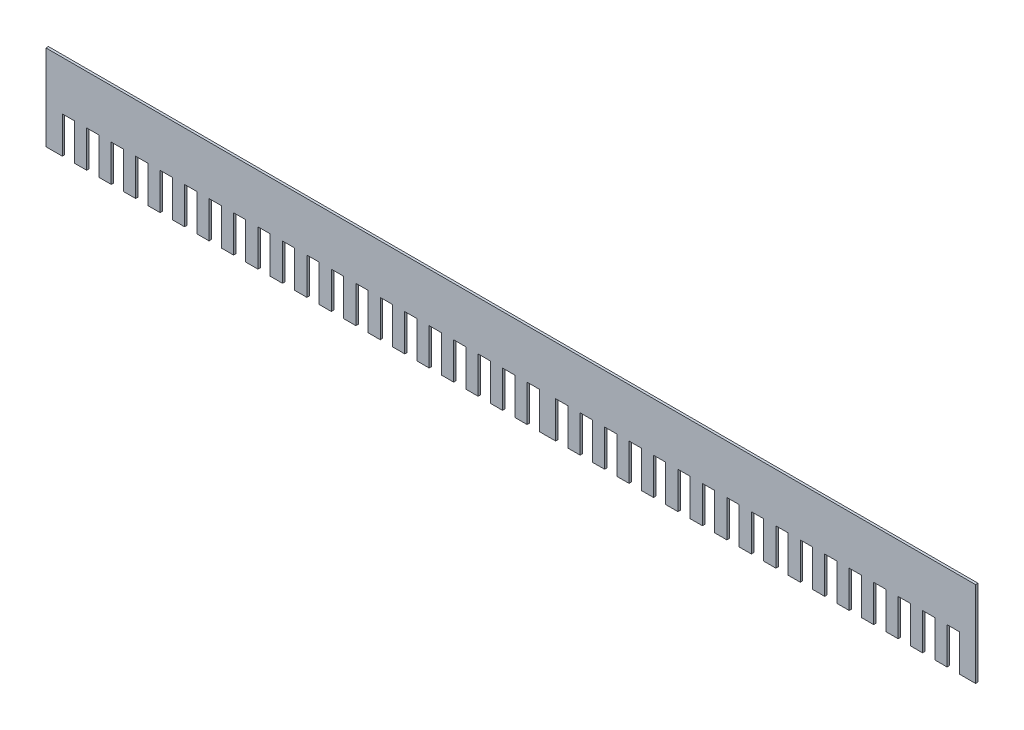
SolidWorks part; units mm, degrees
ref_plane "Front Plane" through (0, 0, 0) normal (0, 0, 1) x (1, 0, 0)
ref_plane "Top Plane" through (0, 0, 0) normal (0, 1, 0) x (1, 0, 0)
ref_plane "Right Plane" through (0, 0, 0) normal (1, 0, 0) x (0, 0, -1)
sketch "Sketch1" plane through (0, 0, 0) normal (0, 0, 1) x (1, 0, 0)
  line L0 (-180.8196, -15.4651) -> (-180.8196, -0.4651)
  line L1 (-202.4725, 19.5349) -> (177.5275, 19.5349)
  line L2 (-202.4725, 19.5349) -> (-202.4725, -15.4651)
  line L3 (-202.4725, -15.4651) -> (177.5275, -15.4651)
  line L5 (-195.8196, -15.4651) -> (-190.8196, -15.4651)
  line L6 (-195.8196, -15.4651) -> (-195.8196, -0.4651)
  line L7 (-195.8196, -0.4651) -> (-190.8196, -0.4651)
  line L8 (-190.8196, -15.4651) -> (-190.8196, -0.4651)
  line L9 (-185.8196, -15.4651) -> (-185.8196, -0.4651)
  line L10 (-185.8196, -0.4651) -> (-180.8196, -0.4651)
  line L11 (-180.8196, -15.4651) -> (-180.8196, -0.4651)
  line L12 (-185.8196, -15.4651) -> (-185.8196, -0.4651)
  line L13 (-185.8196, -0.4651) -> (-180.8196, -0.4651)
  line L14 (-175.8196, -15.4651) -> (-175.8196, -0.4651)
  line L15 (-175.8196, -0.4651) -> (-170.8196, -0.4651)
  line L16 (-170.8196, -15.4651) -> (-170.8196, -0.4651)
  line L17 (-180.8196, -15.4651) -> (-180.8196, -0.4651)
  line L18 (-185.8196, -15.4651) -> (-185.8196, -0.4651)
  line L19 (-185.8196, -0.4651) -> (-180.8196, -0.4651)
  line L20 (-175.8196, -15.4651) -> (-175.8196, -0.4651)
  line L21 (-175.8196, -0.4651) -> (-170.8196, -0.4651)
  line L22 (-170.8196, -15.4651) -> (-170.8196, -0.4651)
  line L23 (-165.8196, -15.4651) -> (-165.8196, -0.4651)
  line L24 (-165.8196, -0.4651) -> (-160.8196, -0.4651)
  line L25 (-160.8196, -15.4651) -> (-160.8196, -0.4651)
  line L26 (-180.8196, -15.4651) -> (-180.8196, -0.4651)
  line L27 (-185.8196, -15.4651) -> (-185.8196, -0.4651)
  line L28 (-185.8196, -0.4651) -> (-180.8196, -0.4651)
  line L29 (-175.8196, -15.4651) -> (-175.8196, -0.4651)
  line L30 (-175.8196, -0.4651) -> (-170.8196, -0.4651)
  line L31 (-170.8196, -15.4651) -> (-170.8196, -0.4651)
  line L32 (-165.8196, -15.4651) -> (-165.8196, -0.4651)
  line L33 (-165.8196, -0.4651) -> (-160.8196, -0.4651)
  line L34 (-160.8196, -15.4651) -> (-160.8196, -0.4651)
  line L35 (-155.8196, -15.4651) -> (-155.8196, -0.4651)
  line L36 (-155.8196, -0.4651) -> (-150.8196, -0.4651)
  line L37 (-150.8196, -15.4651) -> (-150.8196, -0.4651)
  line L38 (-145.8196, -15.4651) -> (-145.8196, -0.4651)
  line L39 (-145.8196, -0.4651) -> (-140.8196, -0.4651)
  line L40 (-140.8196, -15.4651) -> (-140.8196, -0.4651)
  line L41 (-135.8196, -15.4651) -> (-135.8196, -0.4651)
  line L42 (-135.8196, -0.4651) -> (-130.8196, -0.4651)
  line L43 (-130.8196, -15.4651) -> (-130.8196, -0.4651)
  line L44 (-135.8196, -15.4651) -> (-135.8196, -0.4651)
  line L45 (-135.8196, -0.4651) -> (-130.8196, -0.4651)
  line L46 (-130.8196, -15.4651) -> (-130.8196, -0.4651)
  line L47 (-125.8196, -15.4651) -> (-125.8196, -0.4651)
  line L48 (-125.8196, -0.4651) -> (-120.8196, -0.4651)
  line L49 (-120.8196, -15.4651) -> (-120.8196, -0.4651)
  line L50 (-135.8196, -15.4651) -> (-135.8196, -0.4651)
  line L51 (-135.8196, -0.4651) -> (-130.8196, -0.4651)
  line L52 (-130.8196, -15.4651) -> (-130.8196, -0.4651)
  line L53 (-125.8196, -15.4651) -> (-125.8196, -0.4651)
  line L54 (-125.8196, -0.4651) -> (-120.8196, -0.4651)
  line L55 (-120.8196, -15.4651) -> (-120.8196, -0.4651)
  line L56 (-115.8196, -15.4651) -> (-115.8196, -0.4651)
  line L57 (-115.8196, -0.4651) -> (-110.8196, -0.4651)
  line L58 (-110.8196, -15.4651) -> (-110.8196, -0.4651)
  line L59 (-105.8196, -15.4651) -> (-105.8196, -0.4651)
  line L60 (-105.8196, -0.4651) -> (-100.8196, -0.4651)
  line L61 (-100.8196, -15.4651) -> (-100.8196, -0.4651)
  line L62 (-95.8196, -15.4651) -> (-95.8196, -0.4651)
  line L63 (-95.8196, -0.4651) -> (-90.8196, -0.4651)
  line L64 (-90.8196, -15.4651) -> (-90.8196, -0.4651)
  line L65 (-105.8196, -15.4651) -> (-105.8196, -0.4651)
  line L66 (-100.8196, -15.4651) -> (-100.8196, -0.4651)
  line L67 (-85.8196, -15.4651) -> (-85.8196, -0.4651)
  line L68 (-85.8196, -0.4651) -> (-80.8196, -0.4651)
  line L69 (-80.8196, -15.4651) -> (-80.8196, -0.4651)
  line L70 (-85.8196, -15.4651) -> (-85.8196, -0.4651)
  line L71 (-85.8196, -0.4651) -> (-80.8196, -0.4651)
  line L72 (-80.8196, -15.4651) -> (-80.8196, -0.4651)
  line L73 (-75.8196, -15.4651) -> (-75.8196, -0.4651)
  line L74 (-75.8196, -0.4651) -> (-70.8196, -0.4651)
  line L75 (-70.8196, -15.4651) -> (-70.8196, -0.4651)
  line L76 (-85.8196, -15.4651) -> (-85.8196, -0.4651)
  line L77 (-85.8196, -0.4651) -> (-80.8196, -0.4651)
  line L78 (-80.8196, -15.4651) -> (-80.8196, -0.4651)
  line L79 (-75.8196, -15.4651) -> (-75.8196, -0.4651)
  line L80 (-75.8196, -0.4651) -> (-70.8196, -0.4651)
  line L81 (-70.8196, -15.4651) -> (-70.8196, -0.4651)
  line L82 (-65.8196, -15.4651) -> (-65.8196, -0.4651)
  line L83 (-65.8196, -0.4651) -> (-60.8196, -0.4651)
  line L84 (-60.8196, -15.4651) -> (-60.8196, -0.4651)
  line L85 (-85.8196, -15.4651) -> (-85.8196, -0.4651)
  line L86 (-85.8196, -0.4651) -> (-80.8196, -0.4651)
  line L87 (-80.8196, -15.4651) -> (-80.8196, -0.4651)
  line L88 (-75.8196, -15.4651) -> (-75.8196, -0.4651)
  line L89 (-75.8196, -0.4651) -> (-70.8196, -0.4651)
  line L90 (-70.8196, -15.4651) -> (-70.8196, -0.4651)
  line L91 (-65.8196, -15.4651) -> (-65.8196, -0.4651)
  line L92 (-65.8196, -0.4651) -> (-60.8196, -0.4651)
  line L93 (-60.8196, -15.4651) -> (-60.8196, -0.4651)
  line L94 (-55.8196, -15.4651) -> (-55.8196, -0.4651)
  line L95 (-55.8196, -0.4651) -> (-50.8196, -0.4651)
  line L96 (-50.8196, -15.4651) -> (-50.8196, -0.4651)
  line L97 (-85.8196, -15.4651) -> (-85.8196, -0.4651)
  line L98 (-85.8196, -0.4651) -> (-80.8196, -0.4651)
  line L99 (-80.8196, -15.4651) -> (-80.8196, -0.4651)
  line L100 (-75.8196, -15.4651) -> (-75.8196, -0.4651)
  line L101 (-75.8196, -0.4651) -> (-70.8196, -0.4651)
  line L102 (-70.8196, -15.4651) -> (-70.8196, -0.4651)
  line L103 (-65.8196, -15.4651) -> (-65.8196, -0.4651)
  line L104 (-65.8196, -0.4651) -> (-60.8196, -0.4651)
  line L105 (-60.8196, -15.4651) -> (-60.8196, -0.4651)
  line L106 (-55.8196, -15.4651) -> (-55.8196, -0.4651)
  line L107 (-55.8196, -0.4651) -> (-50.8196, -0.4651)
  line L108 (-50.8196, -15.4651) -> (-50.8196, -0.4651)
  line L109 (-45.8196, -15.4651) -> (-45.8196, -0.4651)
  line L110 (-45.8196, -0.4651) -> (-40.8196, -0.4651)
  line L111 (-40.8196, -15.4651) -> (-40.8196, -0.4651)
  line L112 (-85.8196, -15.4651) -> (-85.8196, -0.4651)
  line L113 (-85.8196, -0.4651) -> (-80.8196, -0.4651)
  line L114 (-80.8196, -15.4651) -> (-80.8196, -0.4651)
  line L115 (-75.8196, -15.4651) -> (-75.8196, -0.4651)
  line L116 (-75.8196, -0.4651) -> (-70.8196, -0.4651)
  line L117 (-70.8196, -15.4651) -> (-70.8196, -0.4651)
  line L118 (-65.8196, -15.4651) -> (-65.8196, -0.4651)
  line L119 (-65.8196, -0.4651) -> (-60.8196, -0.4651)
  line L120 (-60.8196, -15.4651) -> (-60.8196, -0.4651)
  line L121 (-55.8196, -15.4651) -> (-55.8196, -0.4651)
  line L122 (-55.8196, -0.4651) -> (-50.8196, -0.4651)
  line L123 (-50.8196, -15.4651) -> (-50.8196, -0.4651)
  line L124 (-45.8196, -15.4651) -> (-45.8196, -0.4651)
  line L125 (-45.8196, -0.4651) -> (-40.8196, -0.4651)
  line L126 (-40.8196, -15.4651) -> (-40.8196, -0.4651)
  line L127 (-35.8196, -15.4651) -> (-35.8196, -0.4651)
  line L128 (-35.8196, -0.4651) -> (-30.8196, -0.4651)
  line L129 (-30.8196, -15.4651) -> (-30.8196, -0.4651)
  line L130 (-12.4725, 19.5349) -> (-12.4725, -15.4651) construction
  line L131 (5.8747, -15.4651) -> (5.8747, -0.4651)
  line L132 (10.8747, -0.4651) -> (5.8747, -0.4651)
  line L133 (10.8747, -15.4651) -> (10.8747, -0.4651)
  line L134 (15.8747, -15.4651) -> (15.8747, -0.4651)
  line L135 (20.8747, -0.4651) -> (15.8747, -0.4651)
  line L136 (20.8747, -15.4651) -> (20.8747, -0.4651)
  line L137 (25.8747, -15.4651) -> (25.8747, -0.4651)
  line L138 (30.8747, -0.4651) -> (25.8747, -0.4651)
  line L139 (30.8747, -15.4651) -> (30.8747, -0.4651)
  line L140 (35.8747, -15.4651) -> (35.8747, -0.4651)
  line L141 (40.8747, -0.4651) -> (35.8747, -0.4651)
  line L142 (40.8747, -15.4651) -> (40.8747, -0.4651)
  line L143 (45.8747, -15.4651) -> (45.8747, -0.4651)
  line L144 (50.8747, -0.4651) -> (45.8747, -0.4651)
  line L145 (50.8747, -15.4651) -> (50.8747, -0.4651)
  line L146 (55.8747, -15.4651) -> (55.8747, -0.4651)
  line L147 (60.8747, -0.4651) -> (55.8747, -0.4651)
  line L148 (60.8747, -15.4651) -> (60.8747, -0.4651)
  line L149 (15.8747, -15.4651) -> (15.8747, -0.4651)
  line L150 (20.8747, -0.4651) -> (15.8747, -0.4651)
  line L151 (20.8747, -15.4651) -> (20.8747, -0.4651)
  line L152 (25.8747, -15.4651) -> (25.8747, -0.4651)
  line L153 (30.8747, -0.4651) -> (25.8747, -0.4651)
  line L154 (30.8747, -15.4651) -> (30.8747, -0.4651)
  line L155 (35.8747, -15.4651) -> (35.8747, -0.4651)
  line L156 (40.8747, -0.4651) -> (35.8747, -0.4651)
  line L157 (40.8747, -15.4651) -> (40.8747, -0.4651)
  line L158 (45.8747, -15.4651) -> (45.8747, -0.4651)
  line L159 (50.8747, -0.4651) -> (45.8747, -0.4651)
  line L160 (50.8747, -15.4651) -> (50.8747, -0.4651)
  line L161 (55.8747, -15.4651) -> (55.8747, -0.4651)
  line L162 (60.8747, -0.4651) -> (55.8747, -0.4651)
  line L163 (60.8747, -15.4651) -> (60.8747, -0.4651)
  line L164 (25.8747, -15.4651) -> (25.8747, -0.4651)
  line L165 (30.8747, -0.4651) -> (25.8747, -0.4651)
  line L166 (30.8747, -15.4651) -> (30.8747, -0.4651)
  line L167 (35.8747, -15.4651) -> (35.8747, -0.4651)
  line L168 (40.8747, -0.4651) -> (35.8747, -0.4651)
  line L169 (40.8747, -15.4651) -> (40.8747, -0.4651)
  line L170 (45.8747, -15.4651) -> (45.8747, -0.4651)
  line L171 (50.8747, -0.4651) -> (45.8747, -0.4651)
  line L172 (50.8747, -15.4651) -> (50.8747, -0.4651)
  line L173 (55.8747, -15.4651) -> (55.8747, -0.4651)
  line L174 (60.8747, -0.4651) -> (55.8747, -0.4651)
  line L175 (60.8747, -15.4651) -> (60.8747, -0.4651)
  line L176 (35.8747, -15.4651) -> (35.8747, -0.4651)
  line L177 (40.8747, -0.4651) -> (35.8747, -0.4651)
  line L178 (40.8747, -15.4651) -> (40.8747, -0.4651)
  line L179 (45.8747, -15.4651) -> (45.8747, -0.4651)
  line L180 (50.8747, -0.4651) -> (45.8747, -0.4651)
  line L181 (50.8747, -15.4651) -> (50.8747, -0.4651)
  line L182 (55.8747, -15.4651) -> (55.8747, -0.4651)
  line L183 (60.8747, -0.4651) -> (55.8747, -0.4651)
  line L184 (60.8747, -15.4651) -> (60.8747, -0.4651)
  line L185 (45.8747, -15.4651) -> (45.8747, -0.4651)
  line L186 (50.8747, -0.4651) -> (45.8747, -0.4651)
  line L187 (50.8747, -15.4651) -> (50.8747, -0.4651)
  line L188 (55.8747, -15.4651) -> (55.8747, -0.4651)
  line L189 (60.8747, -0.4651) -> (55.8747, -0.4651)
  line L190 (60.8747, -15.4651) -> (60.8747, -0.4651)
  line L191 (55.8747, -15.4651) -> (55.8747, -0.4651)
  line L192 (60.8747, -0.4651) -> (55.8747, -0.4651)
  line L193 (60.8747, -15.4651) -> (60.8747, -0.4651)
  line L194 (75.8747, -15.4651) -> (75.8747, -0.4651)
  line L195 (80.8747, -15.4651) -> (80.8747, -0.4651)
  line L196 (65.8747, -15.4651) -> (65.8747, -0.4651)
  line L197 (70.8747, -0.4651) -> (65.8747, -0.4651)
  line L198 (70.8747, -15.4651) -> (70.8747, -0.4651)
  line L199 (75.8747, -15.4651) -> (75.8747, -0.4651)
  line L200 (80.8747, -0.4651) -> (75.8747, -0.4651)
  line L201 (80.8747, -15.4651) -> (80.8747, -0.4651)
  line L202 (85.8747, -15.4651) -> (85.8747, -0.4651)
  line L203 (90.8747, -0.4651) -> (85.8747, -0.4651)
  line L204 (90.8747, -15.4651) -> (90.8747, -0.4651)
  line L205 (95.8747, -15.4651) -> (95.8747, -0.4651)
  line L206 (100.8747, -0.4651) -> (95.8747, -0.4651)
  line L207 (100.8747, -15.4651) -> (100.8747, -0.4651)
  line L208 (105.8747, -15.4651) -> (105.8747, -0.4651)
  line L209 (110.8747, -0.4651) -> (105.8747, -0.4651)
  line L210 (110.8747, -15.4651) -> (110.8747, -0.4651)
  line L211 (95.8747, -15.4651) -> (95.8747, -0.4651)
  line L212 (100.8747, -0.4651) -> (95.8747, -0.4651)
  line L213 (100.8747, -15.4651) -> (100.8747, -0.4651)
  line L214 (105.8747, -15.4651) -> (105.8747, -0.4651)
  line L215 (110.8747, -0.4651) -> (105.8747, -0.4651)
  line L216 (110.8747, -15.4651) -> (110.8747, -0.4651)
  line L217 (105.8747, -15.4651) -> (105.8747, -0.4651)
  line L218 (110.8747, -0.4651) -> (105.8747, -0.4651)
  line L219 (110.8747, -15.4651) -> (110.8747, -0.4651)
  line L220 (115.8747, -15.4651) -> (115.8747, -0.4651)
  line L221 (120.8747, -0.4651) -> (115.8747, -0.4651)
  line L222 (120.8747, -15.4651) -> (120.8747, -0.4651)
  line L223 (125.8747, -15.4651) -> (125.8747, -0.4651)
  line L224 (130.8747, -0.4651) -> (125.8747, -0.4651)
  line L225 (130.8747, -15.4651) -> (130.8747, -0.4651)
  line L226 (135.8747, -15.4651) -> (135.8747, -0.4651)
  line L227 (140.8747, -0.4651) -> (135.8747, -0.4651)
  line L228 (140.8747, -15.4651) -> (140.8747, -0.4651)
  line L229 (145.8747, -15.4651) -> (145.8747, -0.4651)
  line L230 (150.8747, -0.4651) -> (145.8747, -0.4651)
  line L231 (150.8747, -15.4651) -> (150.8747, -0.4651)
  line L232 (160.8747, -0.4651) -> (155.8747, -0.4651)
  line L233 (160.8747, -15.4651) -> (160.8747, -0.4651)
  line L234 (155.8747, -15.4651) -> (155.8747, -0.4651)
  line L235 (135.8747, -15.4651) -> (135.8747, -0.4651)
  line L236 (140.8747, -0.4651) -> (135.8747, -0.4651)
  line L237 (140.8747, -15.4651) -> (140.8747, -0.4651)
  line L238 (145.8747, -15.4651) -> (145.8747, -0.4651)
  line L239 (150.8747, -0.4651) -> (145.8747, -0.4651)
  line L240 (150.8747, -15.4651) -> (150.8747, -0.4651)
  line L241 (160.8747, -0.4651) -> (155.8747, -0.4651)
  line L242 (160.8747, -15.4651) -> (160.8747, -0.4651)
  line L243 (155.8747, -15.4651) -> (155.8747, -0.4651)
  line L244 (145.8747, -15.4651) -> (145.8747, -0.4651)
  line L245 (150.8747, -0.4651) -> (145.8747, -0.4651)
  line L246 (150.8747, -15.4651) -> (150.8747, -0.4651)
  line L247 (160.8747, -0.4651) -> (155.8747, -0.4651)
  line L248 (160.8747, -15.4651) -> (160.8747, -0.4651)
  line L249 (155.8747, -15.4651) -> (155.8747, -0.4651)
  line L250 (160.8747, -0.4651) -> (155.8747, -0.4651)
  line L251 (160.8747, -15.4651) -> (160.8747, -0.4651)
  line L252 (165.8747, -15.4651) -> (165.8747, -0.4651)
  line L253 (170.8747, -0.4651) -> (165.8747, -0.4651)
  line L254 (170.8747, -15.4651) -> (170.8747, -0.4651)
  line L255 (170.8747, -15.4651) -> (165.8747, -15.4651)
  line L256 (177.5275, 19.5349) -> (177.5275, -15.4651)
  line L257 (155.8747, -15.4651) -> (155.8747, -0.4651)
  line L258 (-25.8196, -15.4651) -> (-25.8196, -0.4651)
  line L259 (-25.8196, -0.4651) -> (-20.8196, -0.4651)
  line L260 (-20.8196, -15.4651) -> (-20.8196, -0.4651)
  line L261 (-15.8196, -15.4651) -> (-15.8196, -0.4651)
  line L262 (-15.8196, -0.4651) -> (-10.8196, -0.4651)
  line L263 (-10.8196, -15.4651) -> (-10.8196, -0.4651)
  line L264 (-5.8196, -15.4651) -> (-5.8196, -0.4651)
  line L265 (-5.8196, -0.4651) -> (-0.8196, -0.4651)
  line L266 (-0.8196, -15.4651) -> (-0.8196, -0.4651)
  dimension "D2" = 190
  dimension "D3" = 2
  dimension "D20" = 35
  dimension "D24" = 380
  dimension "D25" = 5
  dimension "D26" = 15
  dimension "D4" = 2
  dimension "D5" = 2
  dimension "D6" = 2
  dimension "D7" = 2
  dimension "D8" = 2
  dimension "D9" = 2
  dimension "D10" = 2
  dimension "D11" = 2
  dimension "D12" = 2
  dimension "D13" = 2
  dimension "D14" = 2
  dimension "D15" = 2
  dimension "D16" = 2
  dimension "D17" = 2
  dimension "D18" = 2
  dimension "D19" = 2
  dimension "D21" = 2
  dimension "D22" = 2
  dimension "D23" = 2
extrude "Boss-Extrude1" add sketch "Sketch1" along normal blind 1 contours L130 L1 L2 L3 L6 L7 L8 L9 L10 L0 L14 L15 L16 L23 L24 L25 L35 L36 L37 L38 L39 L40 L41 L42 L43 L47 L48 L49 L56 L57 L58 L59 L60 L61 L62 L63 L64 L67 L68 L69 | L1 L130 L262 L263 L3 L264 L265 L266 L131 L132 L133 L134 L135 L136 L137 L138 L139 L140 L141 L142 L143 L144 L145 L146 L147 L148 L196 L197 L198 L194 L200 L195 L202 L203 L204 L205 L206 L207 L208 L209
